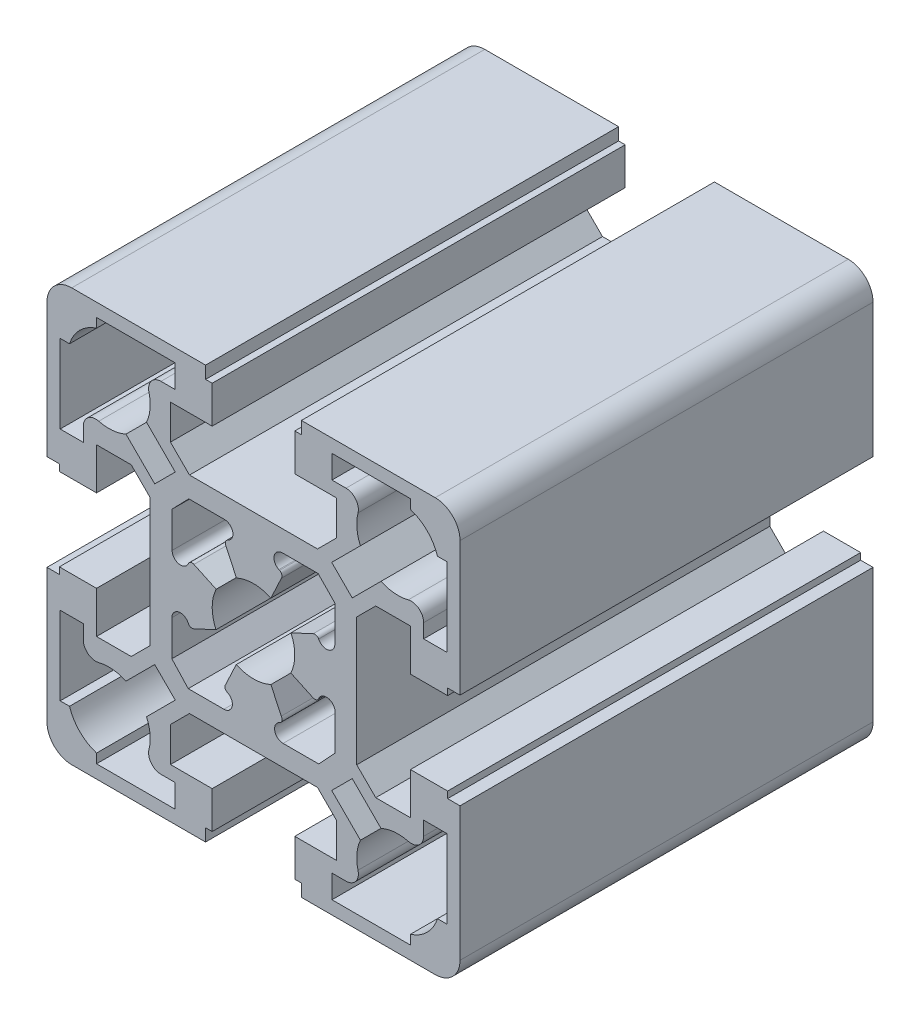
SolidWorks part; units mm, degrees
material "АД31Т ГОСТ 4784-97"
ref_plane "Front Plane" through (0, 0, 0) normal (0, 0, 1) x (1, 0, 0)
ref_plane "Top Plane" through (0, 0, 0) normal (0, 1, 0) x (1, 0, 0)
ref_plane "Right Plane" through (0, 0, 0) normal (1, 0, 0) x (0, 0, -1)
sketch "Sketch1" plane through (0, 0, 0) normal (0, 0, 1) x (1, 0, 0)
  line L0 (3.5053, 9.9658) -> (7.8227, 9.9658)
  line L1 (7.75, 12.5) -> (-7.75, 12.5)
  line L2 (7.9026, -9.9658) -> (3.5852, -9.9658)
  line L3 (-7.75, -12.5) -> (7.75, -12.5)
  line L4 (10.05, -19) -> (5, -19)
  line L5 (5.8, -25) -> (22, -25)
  line L6 (22, 25) -> (5.8, 25)
  line L7 (5, 19) -> (10.05, 19)
  line L8 (-10.05, -19) -> (-10.05, -14.8)
  line L9 (-25, -5.8) -> (-25, -22)
  line L10 (-23.4, -19) -> (-23.4, -9.5)
  line L11 (-22, -25) -> (-5.8, -25)
  line L12 (-9.5, -23.4) -> (-19, -23.4)
  line L13 (-19, -23.4) -> (-19, -22.2697)
  line L14 (-22.2697, -19) -> (-23.4, -19)
  line L15 (5, -19) -> (5, -23.5)
  line L16 (-5, -23.5) -> (-5, -19)
  line L17 (-9.5, -20.6) -> (-9.5, -23.4)
  line L18 (-5.8, -25) -> (-5.8, -23.5)
  line L19 (-5.8, -23.5) -> (-5, -23.5)
  line L20 (5, -23.5) -> (5.8, -23.5)
  line L21 (5.8, -23.5) -> (5.8, -25)
  line L22 (-5, -19) -> (-10.05, -19)
  line L23 (-11.1998, -20.6) -> (-9.5, -20.6)
  line L24 (2.1096, 4.5332) -> (3.3653, 7.2261)
  line L25 (-9.8504, 3.5503) -> (-9.8596, 7.8676)
  line L26 (-3.3235, 7.2452) -> (-2.062, 4.555)
  line L27 (-19, 5) -> (-19, 10.05)
  line L28 (-25, 22) -> (-25, 5.8)
  line L29 (-12.5, 7.75) -> (-12.5, -7.75)
  line L30 (3.3653, -7.2261) -> (2.1096, -4.5332)
  line L31 (-9.8795, -7.8254) -> (-9.8704, -3.5081)
  line L32 (-2.0907, -4.5419) -> (-3.3521, -7.2322)
  line L33 (-12.5, -7.75) -> (-14.8, -10.05)
  line L34 (-15.4339, -12.9467) -> (-11.9554, -9.4681)
  line L35 (-20.6, -9.5) -> (-20.6, -11.1998)
  line L36 (-23.5, -5.8) -> (-25, -5.8)
  line L37 (-14.8, -10.05) -> (-19, -10.05)
  line L38 (-19, -10.05) -> (-19, -5)
  line L39 (-23.5, -5) -> (-23.5, -5.8)
  line L40 (-19, -5) -> (-23.5, -5)
  line L41 (-23.4, -9.5) -> (-20.6, -9.5)
  line L42 (-11.9554, -9.4681) -> (-9.4681, -11.9554)
  line L43 (-10.05, -14.8) -> (-7.75, -12.5)
  line L44 (-9.4681, -11.9554) -> (-12.9467, -15.4339)
  line L45 (-3.5804, -9.9658) -> (-7.8977, -9.9658)
  line L46 (-7.8977, -9.9658) -> (-9.8795, -7.8254)
  line L47 (-3.1727, -7.9957) -> (-3.1444, -8.009)
  line L48 (3.1496, -8.0006) -> (3.1815, -7.9857)
  line L49 (-25, 5.8) -> (-23.5, 5.8)
  line L50 (-23.5, 5.8) -> (-23.5, 5)
  line L51 (-23.5, 5) -> (-19, 5)
  line L52 (-7.9125, -3.0762) -> (-7.8928, -3.1186)
  line L53 (-7.2283, -3.3604) -> (-4.5354, -2.1047)
  line L54 (4.5262, -2.1244) -> (7.2218, -3.3744)
  line L55 (-4.5157, 2.1468) -> (-7.2086, 3.4025)
  line L56 (-7.873, 3.1607) -> (-7.8927, 3.1184)
  line L57 (7.2314, 3.3538) -> (4.5359, 2.1038)
  line L58 (-10.05, 14.8) -> (-10.05, 19)
  line L59 (-23.4, 9.5) -> (-23.4, 19)
  line L60 (-14.8, 10.05) -> (-12.5, 7.75)
  line L61 (-11.9554, 9.4681) -> (-15.4339, 12.9467)
  line L62 (-19, 10.05) -> (-14.8, 10.05)
  line L63 (-20.6, 11.1998) -> (-20.6, 9.5)
  line L64 (-20.6, 9.5) -> (-23.4, 9.5)
  line L65 (-7.75, 12.5) -> (-10.05, 14.8)
  line L66 (-12.9467, 15.4339) -> (-9.4681, 11.9554)
  line L67 (-9.8596, 7.8676) -> (-7.8332, 9.9658)
  line L68 (-7.8332, 9.9658) -> (-3.5158, 9.9658)
  line L69 (-3.0799, 8.009) -> (-3.1275, 7.9867)
  line L70 (-9.4681, 11.9554) -> (-11.9554, 9.4681)
  line L71 (3.164, 7.9635) -> (3.073, 8.0057)
  line L72 (-5.8, 25) -> (-22, 25)
  line L73 (-19, 23.4) -> (-9.5, 23.4)
  line L74 (-19, 22.2697) -> (-19, 23.4)
  line L75 (-23.4, 19) -> (-22.2697, 19)
  line L76 (5.8, 25) -> (5.8, 23.5)
  line L77 (-5.8, 23.5) -> (-5.8, 25)
  line L78 (-10.05, 19) -> (-5, 19)
  line L79 (-5, 19) -> (-5, 23.5)
  line L80 (-5, 23.5) -> (-5.8, 23.5)
  line L81 (-9.5, 23.4) -> (-9.5, 20.6)
  line L82 (-9.5, 20.6) -> (-11.1998, 20.6)
  line L83 (5.8, 23.5) -> (5, 23.5)
  line L84 (5, 23.5) -> (5, 19)
  line L85 (25, -22) -> (25, -5.8)
  line L86 (23.4, -9.5) -> (23.4, -19)
  line L87 (10.05, -14.8) -> (10.05, -19)
  line L88 (9.5, -23.4) -> (9.5, -20.6)
  line L89 (19, -23.4) -> (9.5, -23.4)
  line L90 (19, -22.2697) -> (19, -23.4)
  line L91 (9.5, -20.6) -> (11.1998, -20.6)
  line L92 (23.4, -19) -> (22.2697, -19)
  line L93 (25, 5.8) -> (25, 22)
  line L94 (19, 10.05) -> (19, 5)
  line L95 (9.8596, 7.8778) -> (9.8504, 3.5605)
  line L96 (12.5, -7.75) -> (12.5, 7.75)
  line L97 (9.873, -3.5146) -> (9.8913, -7.8318)
  line L98 (20.6, -11.1998) -> (20.6, -9.5)
  line L99 (9.4681, -11.9554) -> (11.9554, -9.4681)
  line L100 (11.9554, -9.4681) -> (15.4339, -12.9467)
  line L101 (12.9467, -15.4339) -> (9.4681, -11.9554)
  line L102 (7.75, -12.5) -> (10.05, -14.8)
  line L103 (19, -10.05) -> (14.8, -10.05)
  line L104 (14.8, -10.05) -> (12.5, -7.75)
  line L105 (9.8913, -7.8318) -> (7.9026, -9.9658)
  line L106 (25, -5.8) -> (23.5, -5.8)
  line L107 (23.5, -5.8) -> (23.5, -5)
  line L108 (20.6, -9.5) -> (23.4, -9.5)
  line L109 (19, -5) -> (19, -10.05)
  line L110 (23.5, -5) -> (19, -5)
  line L111 (7.8857, -3.1312) -> (7.907, -3.0853)
  line L112 (7.8866, 3.1295) -> (7.8954, 3.1106)
  line L113 (23.5, 5) -> (23.5, 5.8)
  line L114 (23.5, 5.8) -> (25, 5.8)
  line L115 (19, 5) -> (23.5, 5)
  line L116 (23.4, 19) -> (23.4, 9.5)
  line L117 (10.05, 19) -> (10.05, 14.8)
  line L118 (9.4681, 11.9554) -> (12.9467, 15.4339)
  line L119 (15.4339, 12.9467) -> (11.9554, 9.4681)
  line L120 (10.05, 14.8) -> (7.75, 12.5)
  line L121 (14.8, 10.05) -> (19, 10.05)
  line L122 (12.5, 7.75) -> (14.8, 10.05)
  line L123 (11.9554, 9.4681) -> (9.4681, 11.9554)
  line L124 (7.8227, 9.9658) -> (9.8596, 7.8778)
  line L125 (23.4, 9.5) -> (20.6, 9.5)
  line L126 (20.6, 9.5) -> (20.6, 11.1998)
  line L127 (9.5, 23.4) -> (19, 23.4)
  line L128 (11.1998, 20.6) -> (9.5, 20.6)
  line L129 (9.5, 20.6) -> (9.5, 23.4)
  line L130 (22.2697, 19) -> (23.4, 19)
  line L131 (19, 23.4) -> (19, 22.2697)
  line L132 (0, 33.4874) -> (0, -33.1097) construction
  line L133 (-40.5374, 0) -> (39.9079, 0) construction
  arc A0 (7.8954, 3.1106) -> (7.2314, 3.3538) centre (7.4418, 2.9002) ccw
  arc A1 (7.2218, -3.3744) -> (7.8857, -3.1312) centre (7.4321, -2.9208) ccw
  arc A2 (-12.6537, -18.7308) -> (-12.9467, -15.4339) centre (-17.5, -17.5) ccw
  arc A3 (-22.2697, -19) -> (-19, -22.2697) centre (-17.5, -17.5) ccw
  arc A4 (-25, -22) -> (-22, -25) centre (-22, -22) ccw
  arc A5 (-12.6537, -18.7308) -> (-11.1998, -20.6) centre (-11.1998, -19.1) ccw
  arc A6 (-2.0907, -4.5419) -> (2.1096, -4.5332) centre (0, 0) ccw
  arc A7 (-20.6, -11.1998) -> (-18.7308, -12.6537) centre (-19.1, -11.1998) ccw
  arc A8 (-15.4339, -12.9467) -> (-18.7308, -12.6537) centre (-17.5, -17.5) ccw
  arc A9 (-3.5804, -9.9658) -> (-3.1444, -8.009) centre (-3.5804, -8.9388) ccw
  arc A10 (-3.3521, -7.2322) -> (-3.1727, -7.9957) centre (-2.9605, -7.543) ccw
  arc A11 (3.1496, -8.0006) -> (3.5852, -9.9658) centre (3.5852, -8.9349) ccw
  arc A12 (3.1815, -7.9857) -> (3.3653, -7.2261) centre (2.9702, -7.5325) ccw
  arc A13 (-4.5157, 2.1468) -> (-4.5354, -2.1047) centre (0, 0) ccw
  arc A14 (4.5262, -2.1244) -> (4.5359, 2.1038) centre (0, 0) ccw
  arc A15 (-7.9125, -3.0762) -> (-9.8704, -3.5081) centre (-8.8434, -3.5103) ccw
  arc A16 (-7.8928, -3.1186) -> (-7.2283, -3.3604) centre (-7.4396, -2.9073) ccw
  arc A17 (-7.2086, 3.4025) -> (-7.873, 3.1607) centre (-7.4199, 2.9494) ccw
  arc A18 (-9.8504, 3.5503) -> (-7.8927, 3.1184) centre (-8.8235, 3.5524) ccw
  arc A19 (2.1096, 4.5332) -> (-2.062, 4.555) centre (0, 0) ccw
  arc A20 (-12.9467, 15.4339) -> (-12.6537, 18.7308) centre (-17.5, 17.5) ccw
  arc A21 (-18.7308, 12.6537) -> (-15.4339, 12.9467) centre (-17.5, 17.5) ccw
  arc A22 (-18.7308, 12.6537) -> (-20.6, 11.1998) centre (-19.1, 11.1998) ccw
  arc A23 (-3.0799, 8.009) -> (-3.5158, 9.9658) centre (-3.5158, 8.9388) ccw
  arc A24 (-3.1275, 7.9867) -> (-3.3235, 7.2452) centre (-2.9152, 7.534) ccw
  arc A25 (3.3653, 7.2261) -> (3.164, 7.9635) centre (2.9536, 7.5099) ccw
  arc A26 (3.5053, 9.9658) -> (3.073, 8.0057) centre (3.5053, 8.9381) ccw
  arc A27 (-22, 25) -> (-25, 22) centre (-22, 22) ccw
  arc A28 (-19, 22.2697) -> (-22.2697, 19) centre (-17.5, 17.5) ccw
  arc A29 (-11.1998, 20.6) -> (-12.6537, 18.7308) centre (-11.1998, 19.1) ccw
  arc A30 (12.9467, -15.4339) -> (12.6537, -18.7308) centre (17.5, -17.5) ccw
  arc A31 (22, -25) -> (25, -22) centre (22, -22) ccw
  arc A32 (19, -22.2697) -> (22.2697, -19) centre (17.5, -17.5) ccw
  arc A33 (11.1998, -20.6) -> (12.6537, -18.7308) centre (11.1998, -19.1) ccw
  arc A34 (18.7308, -12.6537) -> (15.4339, -12.9467) centre (17.5, -17.5) ccw
  arc A35 (18.7308, -12.6537) -> (20.6, -11.1998) centre (19.1, -11.1998) ccw
  arc A36 (9.873, -3.5146) -> (7.907, -3.0853) centre (8.8422, -3.5189) ccw
  arc A37 (7.8866, 3.1295) -> (9.8504, 3.5605) centre (8.8207, 3.5626) ccw
  arc A38 (12.6537, 18.7308) -> (12.9467, 15.4339) centre (17.5, 17.5) ccw
  arc A39 (15.4339, 12.9467) -> (18.7308, 12.6537) centre (17.5, 17.5) ccw
  arc A40 (20.6, 11.1998) -> (18.7308, 12.6537) centre (19.1, 11.1998) ccw
  arc A41 (25, 22) -> (22, 25) centre (22, 22) ccw
  arc A42 (12.6537, 18.7308) -> (11.1998, 20.6) centre (11.1998, 19.1) ccw
  arc A43 (22.2697, 19) -> (19, 22.2697) centre (17.5, 17.5) ccw
  dimension "D3" = 10
  dimension "D1" = 50
  dimension "D2" = 50
  dimension "D4" = 10
  dimension "D5" = 10
extrude "Base-Extrude" add sketch "Sketch1" against normal blind 50
